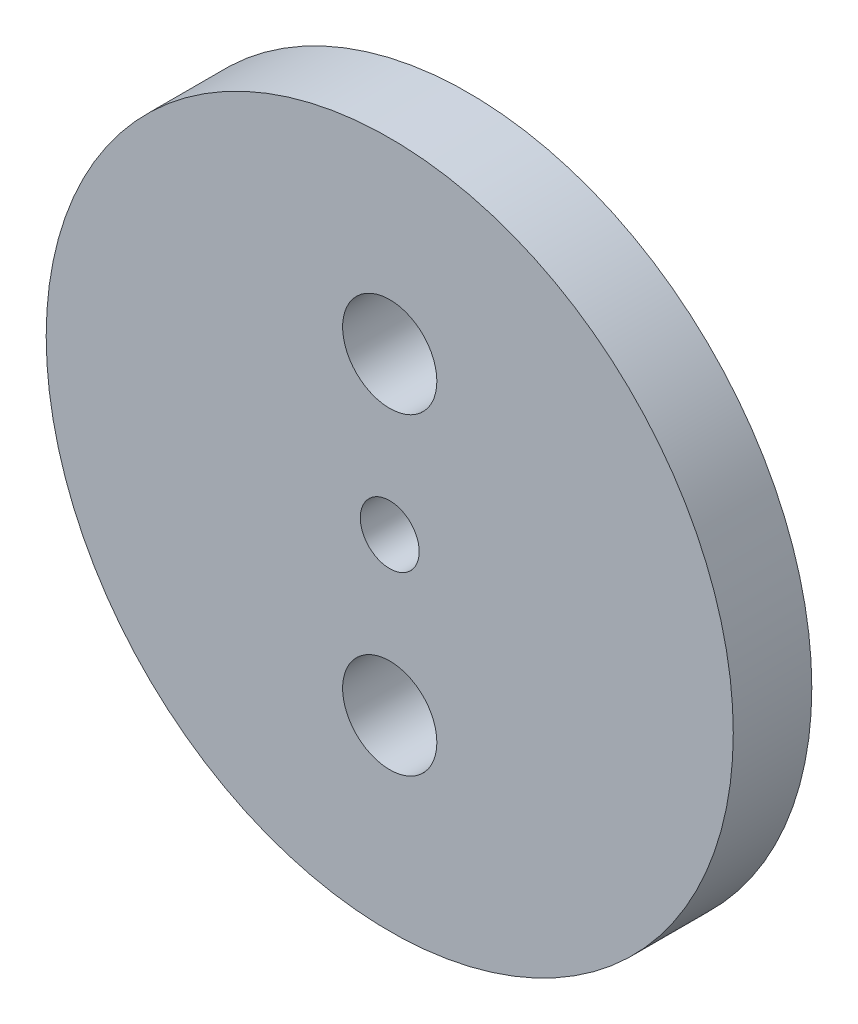
SolidWorks part; units mm, degrees
ref_plane "Front Plane" through (0, 0, 0) normal (0, 0, 1) x (1, 0, 0)
ref_plane "Top Plane" through (0, 0, 0) normal (0, 1, 0) x (1, 0, 0)
ref_plane "Right Plane" through (0, 0, 0) normal (1, 0, 0) x (0, 0, -1)
sketch "Sketch1" plane through (0, 0, 0) normal (0, 0, 1) x (1, 0, 0)
  line L0 (0, 7.97) -> (0, -7.97) construction
  circle A0 centre (0, 0) radius 17.5
  circle A1 centre (0, 7.97) radius 2.4
  circle A2 centre (0, -7.97) radius 2.4
  circle A3 centre (0, 0) radius 1.5
  dimension "D1" = 35
  dimension "D2" = 15.94
  dimension "D4" = 4.8
  dimension "D5" = 3
  dimension "D3" = 7.97
extrude "Boss-Extrude1" add sketch "Sketch1" along normal blind 4
